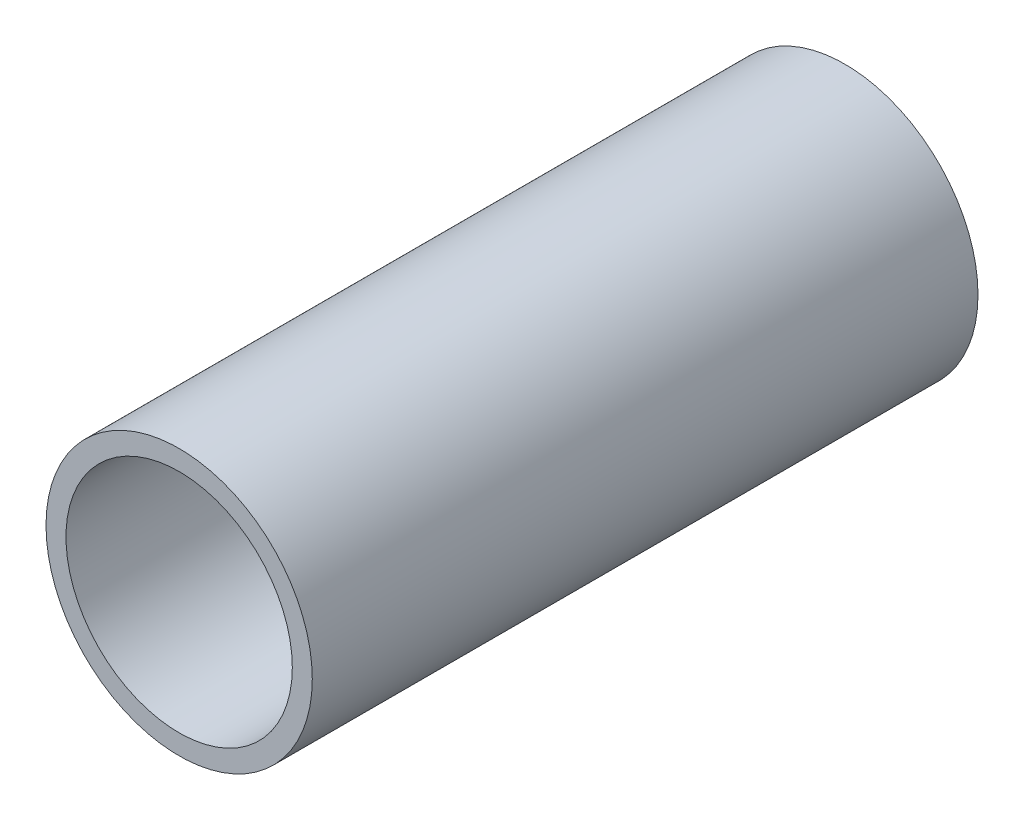
SolidWorks part; units mm, degrees
material "6063-T6"
ref_plane "Спереди" through (0, 0, 0) normal (0, 0, 1) x (1, 0, 0)
ref_plane "Сверху" through (0, 0, 0) normal (0, 1, 0) x (1, 0, 0)
ref_plane "Справа" through (0, 0, 0) normal (1, 0, 0) x (0, 0, -1)
sketch "Эскиз1" plane through (0, 0, 0) normal (0, 0, 1) x (1, 0, 0)
  circle A0 centre (0, 0) radius 20
  circle A1 centre (0, 0) radius 17
  dimension "D1" = 3
  dimension "D2" = 40
extrude "Бобышка-Вытянуть1" add sketch "Эскиз1" against normal blind 100
